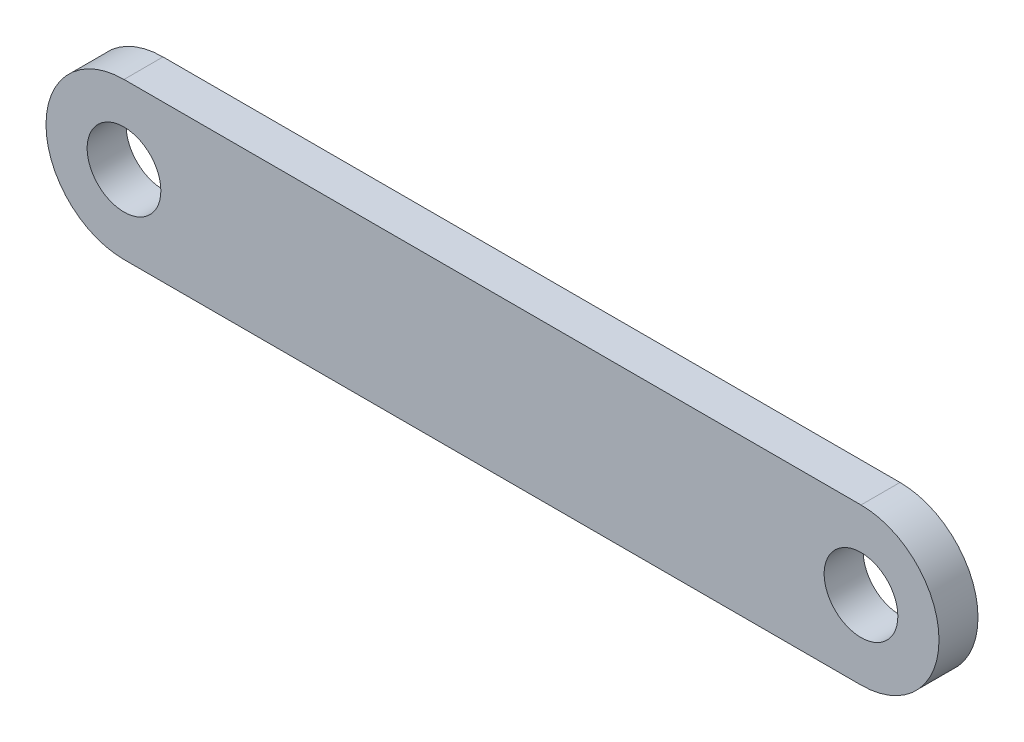
SolidWorks part; units mm, degrees
ref_plane "Front Plane" through (0, 0, 0) normal (0, 0, 1) x (1, 0, 0)
ref_plane "Top Plane" through (0, 0, 0) normal (0, 1, 0) x (1, 0, 0)
ref_plane "Right Plane" through (0, 0, 0) normal (1, 0, 0) x (0, 0, -1)
sketch "Sketch1" plane through (0, 0, 0) normal (0, 0, 1) x (1, 0, 0)
  line L0 (60, 6.35) -> (0, 6.35)
  line L1 (0, -6.35) -> (60, -6.35)
  circle A0 centre (0, 0) radius 3
  circle A1 centre (60, 0) radius 3
  arc A2 (0, 6.35) -> (0, -6.35) centre (0, 0) ccw
  arc A3 (60, -6.35) -> (60, 6.35) centre (60, 0) ccw
  dimension "D1" = 6
  dimension "D2" = 12.7
  dimension "D3" = 72.7
  dimension "Pitch" = 60
extrude "Extrude1" add sketch "Sketch1" against normal blind 3.175
